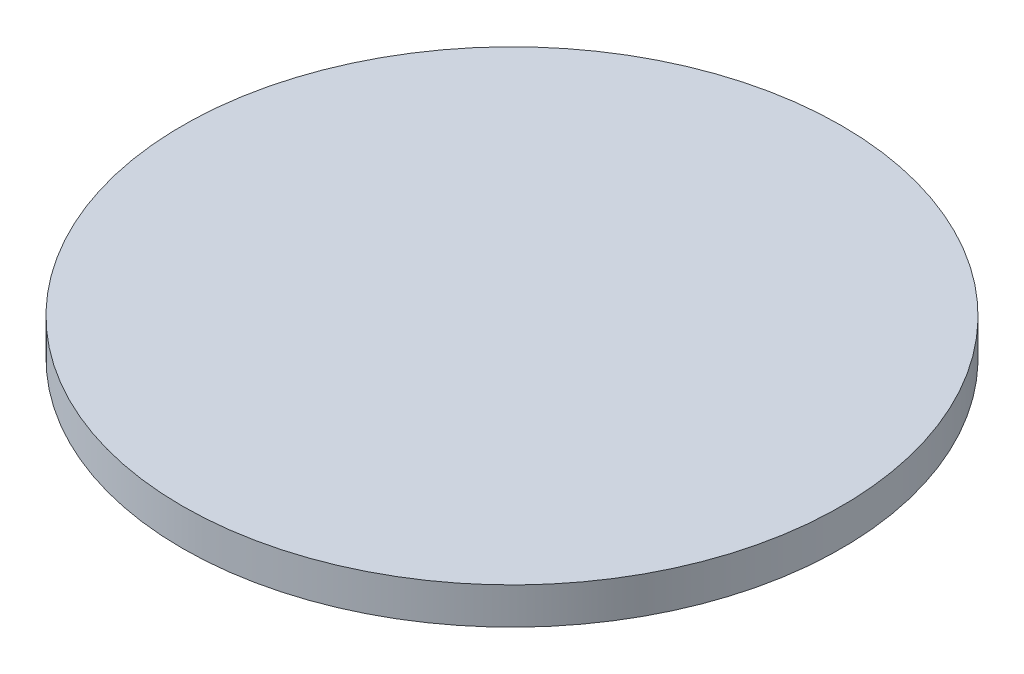
SolidWorks part; units mm, degrees
ref_plane "Front Plane" through (0, 0, 0) normal (0, 0, 1) x (1, 0, 0)
ref_plane "Top Plane" through (0, 0, 0) normal (0, 1, 0) x (1, 0, 0)
ref_plane "Right Plane" through (0, 0, 0) normal (1, 0, 0) x (0, 0, -1)
sketch "Sketch1" plane through (0, 0, 0) normal (0, 1, 0) x (1, 0, 0)
  circle A0 centre (0, 0) radius 27
  dimension "D1" = 54
extrude "Boss-Extrude1" add sketch "Sketch1" along normal blind 3
